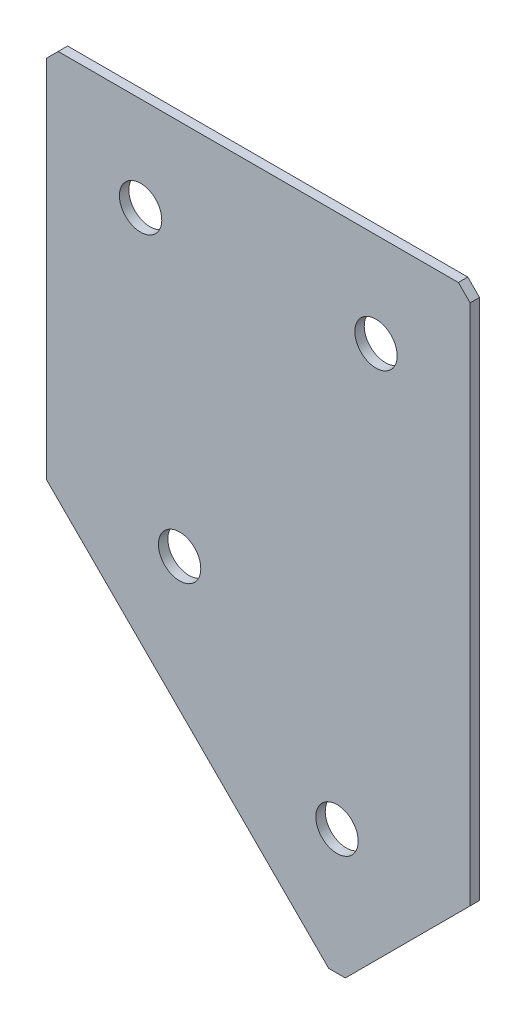
SolidWorks part; units mm, degrees
material "Простая углеродистая сталь"
ref_plane "Спереди" through (0, 0, 0) normal (0, 0, 1) x (1, 0, 0)
ref_plane "Сверху" through (0, 0, 0) normal (0, 1, 0) x (1, 0, 0)
ref_plane "Справа" through (0, 0, 0) normal (1, 0, 0) x (0, 0, -1)
sketch "Эскиз3" plane through (0, 0, 0) normal (0, 0, -1) x (1, 0, 0)
  line L0 (0, 0) -> (90, 0)
  line L1 (90, 0) -> (90, 113.4315)
  line L2 (0, 0) -> (0, 80)
  line L3 (0, 80) -> (61.7157, 141.7157)
  line L4 (61.7157, 141.7157) -> (90, 113.4315)
  dimension "D1" = 90
  dimension "D2" = 80
  dimension "D3" = 40
  dimension "D4" = 45
  dimension "D5" = 113.4315
extrude "Бобышка-Вытянуть1" add sketch "Эскиз3" along normal blind 2
hole_wizard "Отверстие с зазором M81" positions "Эскиз4" profile "Эскиз5" hole size "M8" standard "DIN" end condition through all
sketch "Эскиз4" plane through (0, 0, -2) normal (0, 0, -1) x (1, 0, 0)
  line L0 (28.2843, 80) -> (61.7157, 113.4315) construction
  line L2 (61.7157, 141.7157) -> (0, 80) construction
  line L3 (20, 20) -> (70, 20) construction
  line L5 (0, 0) -> (90, 0) construction
  line L6 (0, 80) -> (0, 0) construction
  line L7 (90, 0) -> (90, 113.4315) construction
  line L8 (90, 113.4315) -> (61.7157, 141.7157) construction
  line L9 (28.2843, 80) -> (0, 51.7157) construction
  point P0 (20, 20)
  point P2 (70, 20)
  point P4 (28.2843, 80)
  point P6 (61.7157, 113.4315)
  point P16 (20, 20)
  dimension "D1" = 20
  dimension "D2" = 20
  dimension "D3" = 20
  dimension "D4" = 20
  dimension "D5" = 20
  dimension "D6" = 40
  dimension "D7" = 47.2792
  dimension "D8" = 50
sketch "Эскиз5" plane through (20, -20, -2) normal (1, 0, 0) x (0, 1, 0)
  line L0 (0, 0) -> (0, 2)
  line L1 (0, 2) -> (4.5, 2)
  line L2 (4.5, 2) -> (4.5, 0)
  line L5 (4.5, 0) -> (0, 0)
  line L11 (0, -6.35) -> (0, 107.95) construction
  dimension "Диаметр сквозного отверстия" = 9
  dimension "Глубина сквозного отверстия" = 2
chamfer "Фаска1" distance 2.5 distance2 2.5 3 edges at (61.7157, -141.7157, -1) (90, 0, -1) (0, 0, -1)
